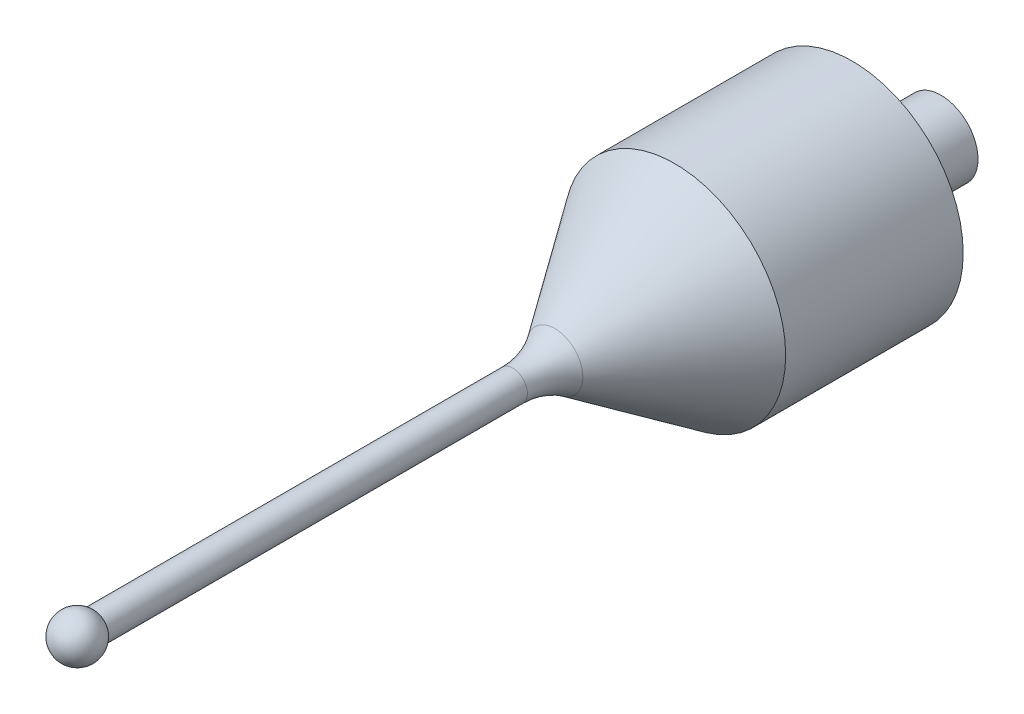
SolidWorks part; units mm, degrees
ref_plane "Front Plane" through (0, 0, 0) normal (0, 0, 1) x (1, 0, 0)
ref_plane "Top Plane" through (0, 0, 0) normal (0, 1, 0) x (1, 0, 0)
ref_plane "Right Plane" through (0, 0, 0) normal (1, 0, 0) x (0, 0, -1)
sketch "Sketch1" plane through (0, 0, 0) normal (0, 1, 0) x (1, 0, 0)
  line L0 (0, 0) -> (0, 11.925)
  line L1 (0, 11.925) -> (2.5, 11.925)
  line L2 (2.5, 11.925) -> (2.5, 5.925)
  line L3 (2.5, 5.925) -> (7.5, 5.925)
  line L6 (1, -15.4607) -> (0, -15.4607)
  line L7 (0, -15.4607) -> (0, 0)
  line L8 (0, 0) -> (0, 24.8059) construction
  line L9 (7.5, 5.925) -> (7.5, -6.075)
  line L10 (7.5, -6.075) -> (1, -15.4607)
  dimension "D1" = 2.5
  dimension "D2" = 6
  dimension "D3" = 12
  dimension "D4" = 1
  dimension "D5" = 5
revolve "Revolve1" add sketch "Sketch1" angle 360 about L8
sketch "Sketch2" plane through (0, 0, 15.4607) normal (0, 0, 1) x (1, 0, 0)
  circle A0 centre (0, 0) radius 1
extrude "Boss-Extrude1" add sketch "Sketch2" along normal blind 30
fillet "Fillet1" radius 5 1 edges at (1, 0, 15.4607)
ref_plane "Plane1" through (0, 0, 46.4607) normal (0, 0, -1) x (-1, 0, 0)
sketch "Sketch4" plane through (0, 0, 46.4607) normal (0, 0, -1) x (-1, 0, 0)
  line L0 (1.5, 0) -> (-1.5, 0) construction
  line L1 (-1.5, 0) -> (1.5, 0)
  arc A2 (-1.5, 0) -> (1.5, 0) centre (0, 0) ccw
  dimension "D1" = 3
revolve "Revolve8" add sketch "Sketch4" angle 360 about L0
